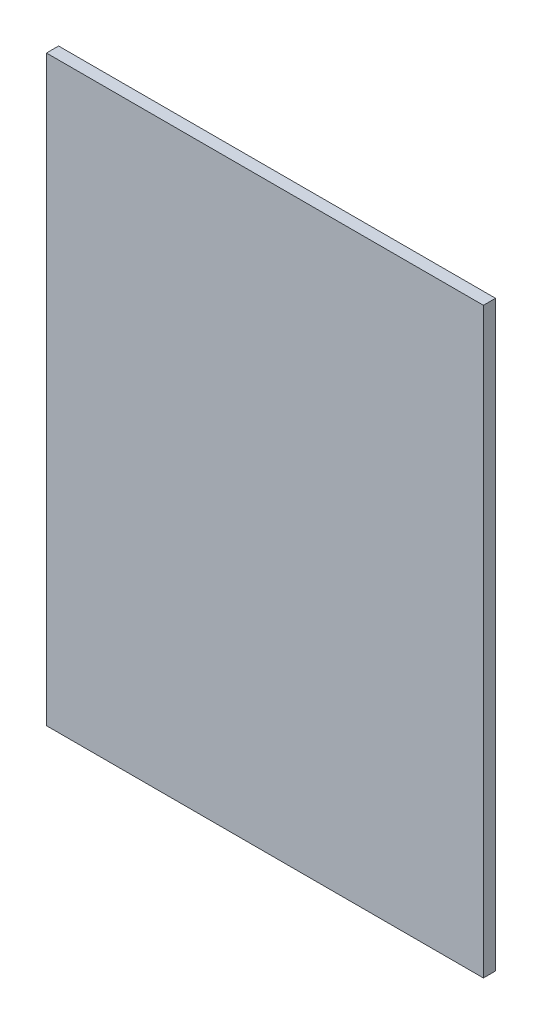
SolidWorks part; units mm, degrees
ref_plane "Front Plane" through (0, 0, 0) normal (0, 0, 1) x (1, 0, 0)
ref_plane "Top Plane" through (0, 0, 0) normal (0, 1, 0) x (1, 0, 0)
ref_plane "Right Plane" through (0, 0, 0) normal (1, 0, 0) x (0, 0, -1)
sketch "Sketch1" plane through (0, 0, 0) normal (0, 0, 1) x (1, 0, 0)
  line L1 (0, 0) -> (914.4, 0)
  line L2 (0, 0) -> (0, -1219.2)
  line L3 (0, -1219.2) -> (914.4, -1219.2)
  line L4 (914.4, 0) -> (914.4, -1219.2)
  dimension "D1" = 1219.2
  dimension "D2" = 914.4
extrude "Boss-Extrude1" add sketch "Sketch1" along normal blind 25.4
